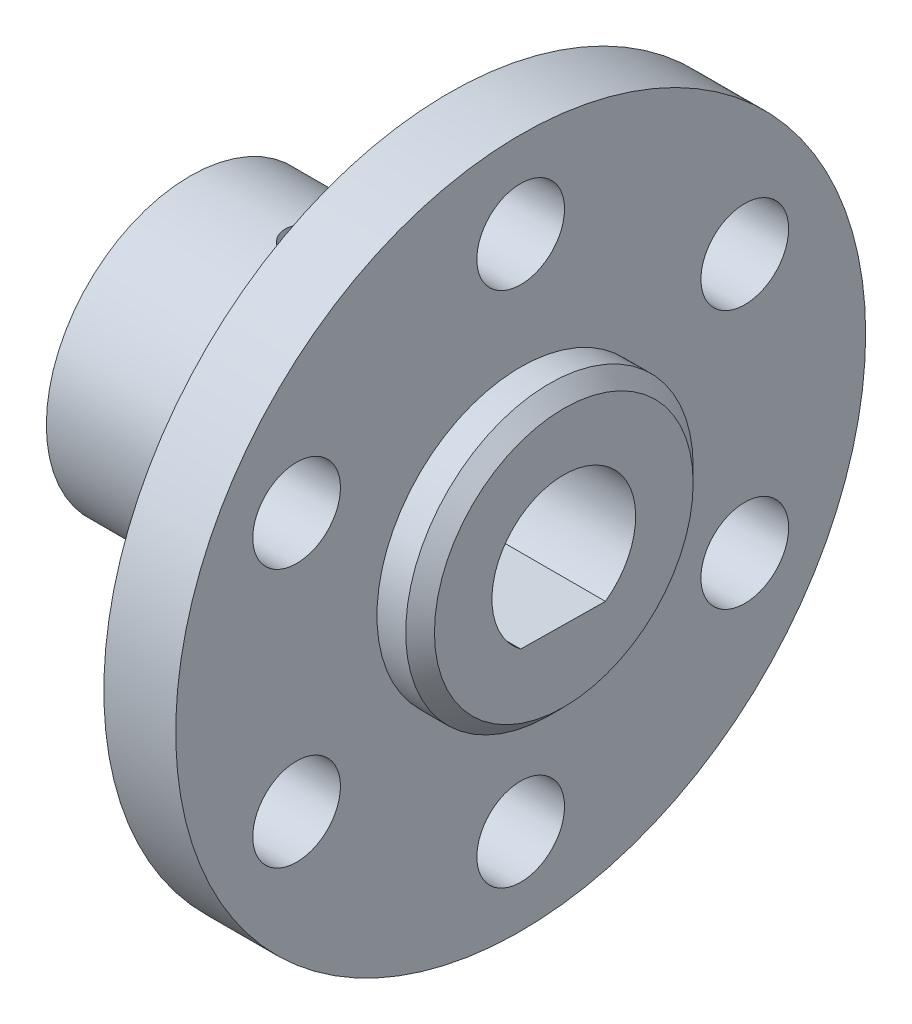
SolidWorks part; units mm, degrees
ref_plane "前视基准面" through (0, 0, 0) normal (0, 0, 1) x (1, 0, 0)
ref_plane "上视基准面" through (0, 0, 0) normal (0, 1, 0) x (1, 0, 0)
ref_plane "右视基准面" through (0, 0, 0) normal (1, 0, 0) x (0, 0, -1)
other "Configuration Table"
sketch "草图1" plane through (0, 0, 0) normal (1, 0, 0) x (0, 0, -1)
  line L0 (0, 0) -> (0, 24) construction
  line L1 (0, 0) -> (-20.7846, 12) construction
  circle A0 centre (0, 0) radius 24
  circle A1 centre (0, 0) radius 18 construction
  circle A2 centre (-15.5885, 9) radius 3.05
  circle A3 centre (0, 18) radius 3.05
  circle A4 centre (15.5885, 9) radius 3.05
  circle A5 centre (15.5885, -9) radius 3.05
  circle A6 centre (0, -18) radius 3.05
  circle A7 centre (-15.5885, -9) radius 3.05
  point P21 (0, 0)
  dimension "D1" = 48
  dimension "D2" = 60
  dimension "D3" = 6.1
  dimension "D4" = 6
extrude "凸台-拉伸1" add sketch "草图1" along normal blind 5
cosmetic thread "装饰螺纹线1" parameters "D2"=7.1
cosmetic thread "装饰螺纹线2" parameters "D2"=7.1
cosmetic thread "装饰螺纹线3" parameters "D2"=7.1
cosmetic thread "装饰螺纹线4" parameters "D2"=7.1
cosmetic thread "装饰螺纹线5" parameters "D2"=7.1
cosmetic thread "装饰螺纹线6" parameters "D2"=7.1
thread "螺纹线1" [suppressed] pitch 0.3175 start angle 0, offset 0, length 5, pitch 0.3175, diameter 6.1
ref_plane "基准面1" through (5, 18, 3.05) normal (0, -1, 0) x (0, 0, 1)
sketch "螺纹线轮廓1" plane through (5, 18, 3.05) normal (0, -1, 0) x (0, 0, 1)
  line L0 (0, 0) -> (0, 0.3175) construction
  line L11 (0, 0) -> (0, 0.2778)
  line L12 (0, 0.2778) -> (-0.1719, 0.1786)
  line L13 (-0.1719, 0.1786) -> (-0.1719, 0.0992)
  line L15 (-0.1719, 0.0992) -> (0, 0)
  line L17 (-0.1719, 0.1389) -> (0, 0.1389) construction
  point P2 (0, 0)
  dimension "Pitch" = 0.3175
  dimension "Profile_Angle" = 60
  dimension "Profile_Land" = 0.0794
  dimension "Profile_Height" = 0.1719
thread "螺纹线2" [suppressed] pitch 0.3175 start angle 0, offset 0, length 5, pitch 0.3175, diameter 6.1
ref_plane "基准面2" through (5, 9, -12.5385) normal (0, -1, 0) x (0, 0, 1)
sketch "螺纹线轮廓2" plane through (5, 9, -12.5385) normal (0, -1, 0) x (0, 0, 1)
  line L0 (0, 0) -> (0, 0.3175) construction
  line L11 (0, 0) -> (0, 0.2778)
  line L12 (0, 0.2778) -> (-0.1719, 0.1786)
  line L13 (-0.1719, 0.1786) -> (-0.1719, 0.0992)
  line L15 (-0.1719, 0.0992) -> (0, 0)
  line L17 (-0.1719, 0.1389) -> (0, 0.1389) construction
  point P2 (0, 0)
  dimension "Pitch" = 0.3175
  dimension "Profile_Angle" = 60
  dimension "Profile_Land" = 0.0794
  dimension "Profile_Height" = 0.1719
thread "螺纹线3" [suppressed] pitch 0.3175 start angle 0, offset 0, length 5, pitch 0.3175, diameter 6.1
ref_plane "基准面3" through (5, -9, -12.5385) normal (0, -1, 0) x (0, 0, 1)
sketch "螺纹线轮廓3" plane through (5, -9, -12.5385) normal (0, -1, 0) x (0, 0, 1)
  line L0 (0, 0) -> (0, 0.3175) construction
  line L11 (0, 0) -> (0, 0.2778)
  line L12 (0, 0.2778) -> (-0.1719, 0.1786)
  line L13 (-0.1719, 0.1786) -> (-0.1719, 0.0992)
  line L15 (-0.1719, 0.0992) -> (0, 0)
  line L17 (-0.1719, 0.1389) -> (0, 0.1389) construction
  point P2 (0, 0)
  dimension "Pitch" = 0.3175
  dimension "Profile_Angle" = 60
  dimension "Profile_Land" = 0.0794
  dimension "Profile_Height" = 0.1719
thread "螺纹线4" [suppressed] pitch 0.3175 start angle 0, offset 0, length 5, pitch 0.3175, diameter 6.1
ref_plane "基准面4" through (5, 9, 18.6385) normal (0, -1, 0) x (0, 0, 1)
sketch "螺纹线轮廓4" plane through (5, 9, 18.6385) normal (0, -1, 0) x (0, 0, 1)
  line L0 (0, 0) -> (0, 0.3175) construction
  line L11 (0, 0) -> (0, 0.2778)
  line L12 (0, 0.2778) -> (-0.1719, 0.1786)
  line L13 (-0.1719, 0.1786) -> (-0.1719, 0.0992)
  line L15 (-0.1719, 0.0992) -> (0, 0)
  line L17 (-0.1719, 0.1389) -> (0, 0.1389) construction
  point P2 (0, 0)
  dimension "Pitch" = 0.3175
  dimension "Profile_Angle" = 60
  dimension "Profile_Land" = 0.0794
  dimension "Profile_Height" = 0.1719
thread "螺纹线5" [suppressed] pitch 0.3175 start angle 0, offset 0, length 5, pitch 0.3175, diameter 6.1
ref_plane "基准面5" through (5, -9, 18.6385) normal (0, -1, 0) x (0, 0, 1)
sketch "螺纹线轮廓5" plane through (5, -9, 18.6385) normal (0, -1, 0) x (0, 0, 1)
  line L0 (0, 0) -> (0, 0.3175) construction
  line L11 (0, 0) -> (0, 0.2778)
  line L12 (0, 0.2778) -> (-0.1719, 0.1786)
  line L13 (-0.1719, 0.1786) -> (-0.1719, 0.0992)
  line L15 (-0.1719, 0.0992) -> (0, 0)
  line L17 (-0.1719, 0.1389) -> (0, 0.1389) construction
  point P2 (0, 0)
  dimension "Pitch" = 0.3175
  dimension "Profile_Angle" = 60
  dimension "Profile_Land" = 0.0794
  dimension "Profile_Height" = 0.1719
thread "螺纹线6" [suppressed] pitch 0.3175 start angle 0, offset 0, length 5, pitch 0.3175, diameter 6.1
ref_plane "基准面6" through (5, -18, 3.05) normal (0, -1, 0) x (0, 0, 1)
sketch "螺纹线轮廓6" plane through (5, -18, 3.05) normal (0, -1, 0) x (0, 0, 1)
  line L0 (0, 0) -> (0, 0.3175) construction
  line L11 (0, 0) -> (0, 0.2778)
  line L12 (0, 0.2778) -> (-0.1719, 0.1786)
  line L13 (-0.1719, 0.1786) -> (-0.1719, 0.0992)
  line L15 (-0.1719, 0.0992) -> (0, 0)
  line L17 (-0.1719, 0.1389) -> (0, 0.1389) construction
  point P2 (0, 0)
  dimension "Pitch" = 0.3175
  dimension "Profile_Angle" = 60
  dimension "Profile_Land" = 0.0794
  dimension "Profile_Height" = 0.1719
sketch "草图14" plane through (5, 0, 0) normal (1, 0, 0) x (0, 0, -1)
  circle A0 centre (0, 0) radius 10
  dimension "D1" = 20
extrude "凸台-拉伸2" add sketch "草图14" along normal blind 3
sketch "草图15" plane through (0, 0, 0) normal (-1, 0, 0) x (0, 0, 1)
  circle A0 centre (0, 0) radius 10
  dimension "D1" = 20
extrude "凸台-拉伸3" add sketch "草图15" along normal blind 18
sketch "草图16" plane through (-18, 0, 0) normal (-1, 0, 0) x (0, 0, 1)
  line L0 (0, -5) -> (0, 5) construction
  line L1 (-3, -4.077) -> (3, -4)
  circle A0 centre (0, 0) radius 5
  circle A1 centre (0, 5) radius 10 construction
  point P5 (0, 0)
  point P10 (0, -4.0385)
  dimension "D1" = 10
  dimension "D2" = 6
extrude "切除-拉伸1" cut sketch "草图16" against normal through all contours L1 A0
fillet "圆角5" radius 3 1 edges at (0, 0, -10)
chamfer "倒角1" distance 1 angle 45 1 edges at (8, 0, -10)
sketch "草图18" plane through (0, -4.0378, 0.0518) normal (0, 0.9999, -0.0128) x (1, 0, 0)
  line L1 (-18, 2.9484) -> (-18, -2.9484) construction
  circle A0 centre (-10, 0) radius 1.5
  dimension "D1" = 3
  dimension "D2" = 8
extrude "切除-拉伸4" cut sketch "草图18" against normal through all and the other way through all
